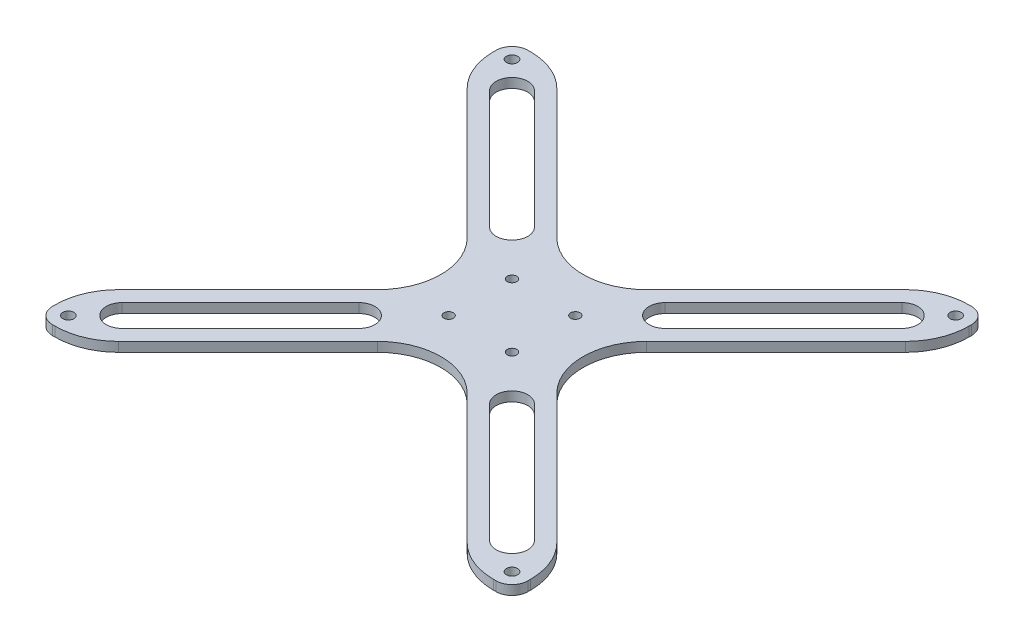
SolidWorks part; units mm, degrees
ref_plane "Front Plane" through (0, 0, 0) normal (0, 0, 1) x (1, 0, 0)
ref_plane "Top Plane" through (0, 0, 0) normal (0, 1, 0) x (1, 0, 0)
ref_plane "Right Plane" through (0, 0, 0) normal (1, 0, 0) x (0, 0, -1)
sketch "Sketch3" plane through (0, 0, 0) normal (0, 1, 0) x (1, 0, 0)
  line L0 (0, 75) -> (0, -75) construction
  line L1 (-75, -75) -> (75, -75)
  line L2 (-75, -75) -> (-75, 75)
  line L3 (-75, 75) -> (75, 75)
  line L4 (75, -75) -> (75, 75)
  line L5 (-75, -75) -> (75, 75) construction
  line L6 (-75, 75) -> (75, -75) construction
  circle A0 centre (-70, 70) radius 1.75
  circle A1 centre (70, -70) radius 1.75
  circle A2 centre (-70, -70) radius 1.75
  circle A3 centre (70, 70) radius 1.75
  circle A4 centre (-10, 10) radius 1.5
  circle A5 centre (10, -10) radius 1.5
  circle A6 centre (-10, -10) radius 1.5
  circle A7 centre (10, 10) radius 1.5
  point P0 (0, 0)
  dimension "D1" = 3.5
  dimension "D2" = 70
  dimension "D3" = 5
  dimension "D4" = 5
  dimension "D5" = 3
  dimension "D6" = 10
extrude "Boss-Extrude2" add sketch "Sketch3" along normal blind 3
sketch "Sketch4" plane through (0, 3, 0) normal (0, 1, 0) x (1, 0, 0)
  line L0 (-75, 75) -> (75, -75) construction
  line L1 (-75, 0) -> (75, 0) construction
  line L2 (-75, 75) -> (-75, -75) construction
  line L3 (75, -75) -> (75, 75) construction
  line L4 (-24.1421, 24.1421) -> (-61.5147, 61.5147) construction
  line L5 (-27.6777, 20.6066) -> (-65.0503, 57.9792)
  line L6 (-20.6066, 27.6777) -> (-57.9792, 65.0503)
  line L7 (0, 75) -> (0, -75) construction
  line L8 (75, 75) -> (-75, 75) construction
  line L9 (-75, -75) -> (75, -75) construction
  line L10 (-75, 60.8579) -> (-14.1421, 0)
  line L11 (-75, 60.8579) -> (-75, -60.8579)
  line L12 (24.1421, 24.1421) -> (61.5147, 61.5147) construction
  line L13 (27.6777, 20.6066) -> (65.0503, 57.9792)
  line L14 (20.6066, 27.6777) -> (57.9792, 65.0503)
  line L15 (24.1421, -24.1421) -> (61.5147, -61.5147) construction
  line L16 (27.6777, -20.6066) -> (65.0503, -57.9792)
  line L17 (20.6066, -27.6777) -> (57.9792, -65.0503)
  line L18 (-24.1421, -24.1421) -> (-61.5147, -61.5147) construction
  line L19 (-27.6777, -20.6066) -> (-65.0503, -57.9792)
  line L20 (-20.6066, -27.6777) -> (-57.9792, -65.0503)
  line L21 (-75, -60.8579) -> (-14.1421, 0)
  line L22 (75, 60.8579) -> (14.1421, 0)
  line L23 (75, -60.8579) -> (14.1421, 0)
  line L24 (75, 60.8579) -> (75, -60.8579)
  line L25 (-60.8579, -75) -> (60.8579, -75)
  line L26 (60.8579, -75) -> (0, -14.1421)
  line L27 (-60.8579, -75) -> (0, -14.1421)
  line L28 (-60.8579, 75) -> (0, 14.1421)
  line L29 (60.8579, 75) -> (0, 14.1421)
  line L30 (-60.8579, 75) -> (60.8579, 75)
  arc A0 (-27.6777, 20.6066) -> (-20.6066, 27.6777) centre (-24.1421, 24.1421) ccw
  arc A1 (-57.9792, 65.0503) -> (-65.0503, 57.9792) centre (-61.5147, 61.5147) ccw
  circle A2 centre (-70, 70) radius 1.75 construction
  circle A3 centre (-10, 10) radius 1.5 construction
  arc A4 (27.6777, 20.6066) -> (20.6066, 27.6777) centre (24.1421, 24.1421) cw
  arc A5 (57.9792, 65.0503) -> (65.0503, 57.9792) centre (61.5147, 61.5147) cw
  arc A6 (27.6777, -20.6066) -> (20.6066, -27.6777) centre (24.1421, -24.1421) ccw
  arc A7 (57.9792, -65.0503) -> (65.0503, -57.9792) centre (61.5147, -61.5147) ccw
  arc A8 (-27.6777, -20.6066) -> (-20.6066, -27.6777) centre (-24.1421, -24.1421) cw
  arc A9 (-57.9792, -65.0503) -> (-65.0503, -57.9792) centre (-61.5147, -61.5147) cw
  point P12 (-42.8284, 42.8284)
  point P31 (42.8284, 42.8284)
  point P38 (42.8284, -42.8284)
  point P45 (-42.8284, -42.8284)
  dimension "D1" = 12
  dimension "D2" = 20
  dimension "D3" = 10
  dimension "D4" = 5
extrude "Cut-Extrude2" cut sketch "Sketch4" against normal up to next
fillet "Fillet2" radius 5 4 edges at (-75, 1.5, -75) (75, 1.5, -75) (75, 1.5, 75) (-75, 1.5, 75)
fillet "Fillet3" radius 20 12 edges at (-75, 1.5, 60.8579) (-60.8579, 1.5, 75) (60.8579, 1.5, 75) (75, 1.5, 60.8579) (75, 1.5, -60.8579) (60.8579, 1.5, -75) (-60.8579, 1.5, -75) (-75, 1.5, -60.8579) (14.1421, 1.5, 0) (0, 1.5, -14.1421) (-14.1421, 1.5, 0) (0, 1.5, 14.1421)
